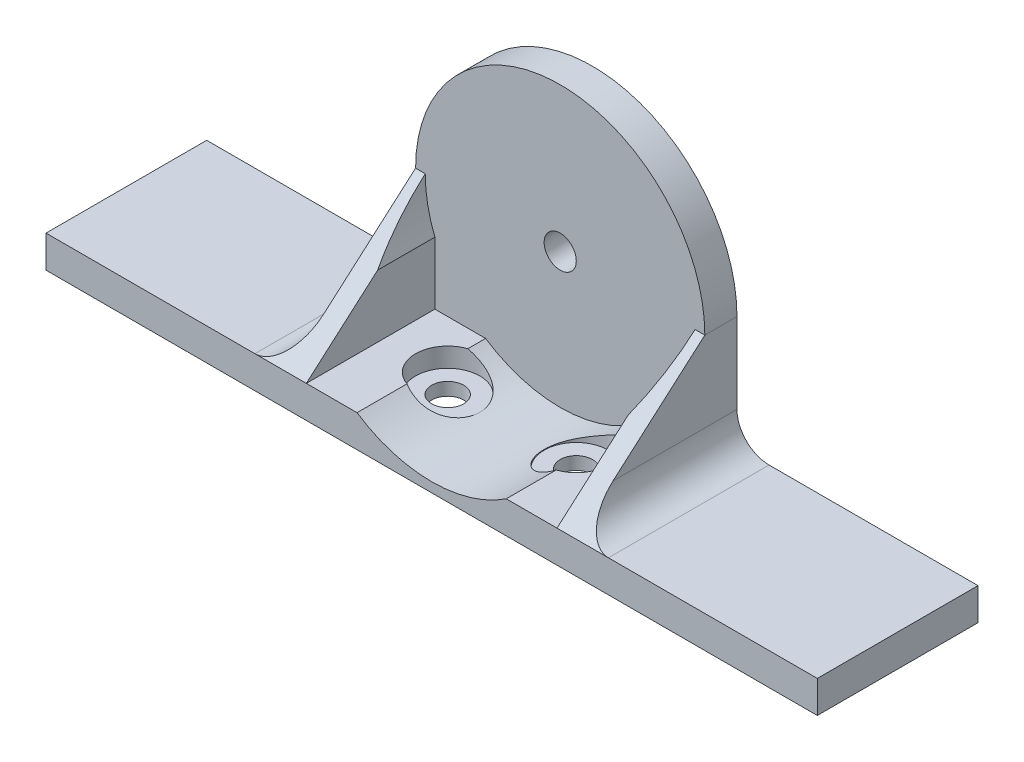
SolidWorks part; units mm, degrees
ref_plane "Front Plane" through (0, 0, 0) normal (0, 0, 1) x (1, 0, 0)
ref_plane "Top Plane" through (0, 0, 0) normal (0, 1, 0) x (1, 0, 0)
ref_plane "Right Plane" through (0, 0, 0) normal (1, 0, 0) x (0, 0, -1)
sketch "Sketch2" plane through (0, 0, 0) normal (0, 0, 1) x (1, 0, 0)
  circle A1 centre (0, 0) radius 22.5
  dimension "D2" = 45
extrude "Boss-Extrude3" add sketch "Sketch2" along normal blind 25
sketch "Sketch6" plane through (0, 0, 0) normal (0, 0, 1) x (1, 0, 0)
  line L1 (-22.5, 0) -> (22.5, 0)
  line L2 (-22.5, 0) -> (-22.5, -22.5)
  line L3 (-22.5, -22.5) -> (22.5, -22.5)
  line L4 (22.5, 0) -> (22.5, -22.5)
  circle A0 centre (0, 0) radius 22.5 construction
extrude "Boss-Extrude4" add sketch "Sketch6" along normal blind 25
sketch "Sketch4" plane through (0, 0, 25) normal (0, 0, 1) x (1, 0, 0)
  circle A0 centre (0, 0) radius 20
  dimension "D1" = 40
extrude "Cut-Extrude1" cut sketch "Sketch4" against normal blind 20
sketch "Sketch5" plane through (0, 0, 0) normal (0, 0, -1) x (-1, 0, 0)
  circle A0 centre (0, 0) radius 2.5
  dimension "D1" = 5
extrude "Cut-Extrude2" cut sketch "Sketch5" against normal up to surface (5 mm away) up to face at (20, 0, 5)
sketch "Sketch7" plane through (0, -22.5, 0) normal (0, -1, 0) x (1, 0, 0)
  line L0 (0, 25) -> (0, 0) construction
  line L1 (-22.5, 25) -> (22.5, 25) construction
  circle A3 centre (-10, 12.5) radius 5
  circle A4 centre (10, 12.5) radius 5
  point P9 (0, 12.5)
  dimension "D2" = 10
  dimension "D4" = 10
extrude "Cut-Extrude6" cut sketch "Sketch7" against normal through all
sketch "Sketch9" plane through (0, -22.5, 0) normal (0, -1, 0) x (1, 0, 0)
  line L0 (0, 25) -> (0, 0) construction
  line L1 (-22.5, 25) -> (22.5, 25) construction
  circle A0 centre (-10, 12.5) radius 5
  circle A1 centre (-10, 12.5) radius 2.5
  circle A2 centre (10, 12.5) radius 2.5
  circle A3 centre (10, 12.5) radius 5
  dimension "D1" = 10
  dimension "D2" = 5
extrude "Boss-Extrude5" add sketch "Sketch9" against normal blind 2
sketch "Sketch14" plane through (22.5, 0, 0) normal (1, 0, 0) x (0, 0, -1)
  line L0 (-25, 0) -> (0, 0) construction
  line L1 (-20, 0) -> (-5, 0)
  line L2 (-20, 2.5) -> (-20, -2.5)
  line L3 (-20, -2.5) -> (-5, -2.5)
  line L4 (-5, 2.5) -> (-5, -2.5)
  line L5 (0, -22.5) -> (0, 0) construction
  line L6 (-25, -22.5) -> (-25, 0) construction
  line L7 (-20, 2.5) -> (-5, 2.5)
  dimension "D1" = 5
  dimension "D2" = 5
  dimension "D3" = 2.5
extrude "Cut-Extrude8" cut sketch "Sketch14" against normal through all contours L7 L4 L3 L2
sketch "Sketch15" plane through (-22.5, 0, 0) normal (-1, 0, 0) x (0, 0, 1)
  line L0 (25, 0) -> (25, -22.5) construction
  line L1 (0, -22.5) -> (25, -22.5)
  line L2 (0, -22.5) -> (0, -17.5)
  line L3 (0, -17.5) -> (25, -17.5)
  line L4 (25, -22.5) -> (25, -17.5)
  dimension "D1" = 5
extrude "Boss-Extrude6" add sketch "Sketch15" along normal blind 37.5
sketch "Sketch16" plane through (22.5, 0, 0) normal (1, 0, 0) x (0, 0, -1)
  line L0 (0, -22.5) -> (0, 0) construction
  line L1 (-25, -22.5) -> (0, -22.5)
  line L2 (-25, -22.5) -> (-25, -17.5)
  line L3 (-25, -17.5) -> (0, -17.5)
  line L4 (0, -22.5) -> (0, -17.5)
  dimension "D1" = 5
extrude "Boss-Extrude7" add sketch "Sketch16" along normal blind 37.5
sketch "Sketch19" plane through (0, 0, 25) normal (0, 0, 1) x (1, 0, 0)
  line L1 (-22.5, -17.5) -> (27.5, -17.5)
  line L2 (-22.5, -17.5) -> (-22.5, 32.5)
  line L3 (-22.5, 32.5) -> (27.5, 32.5)
  line L4 (27.5, -17.5) -> (27.5, 32.5)
  dimension "D1" = 50
  dimension "D2" = 50
extrude "Cut-Extrude9" cut sketch "Sketch19" against normal up to surface (20 mm away) up to face at (2.5, 0, 5)
sketch "Sketch24" plane through (-22.5, 0, 0) normal (-1, 0, 0) x (0, 0, 1)
  line L0 (5, 0) -> (5, -17.5)
  line L1 (5, -17.5) -> (25, -17.5)
  line L2 (25, -17.5) -> (5, 0)
extrude "Boss-Extrude8" add sketch "Sketch24" against normal blind 3
sketch "Sketch25" plane through (22.5, 0, 0) normal (1, 0, 0) x (0, 0, -1)
  line L0 (-5, 0) -> (-25, -17.5)
  line L1 (-25, -17.5) -> (-5, -17.5)
  line L2 (-5, -17.5) -> (-5, 0)
extrude "Boss-Extrude9" add sketch "Sketch25" against normal blind 3
sketch "Sketch22" plane through (0, 0, 5) normal (0, 0, 1) x (1, 0, 0)
  circle A0 centre (0, 0) radius 21
  dimension "D1" = 42
extrude "Cut-Extrude10" cut sketch "Sketch22" along normal through all
fillet "Fillet2" radius 5 2 edges at (-22.5, -17.5, 12.5) (22.5, -17.5, 12.5)
